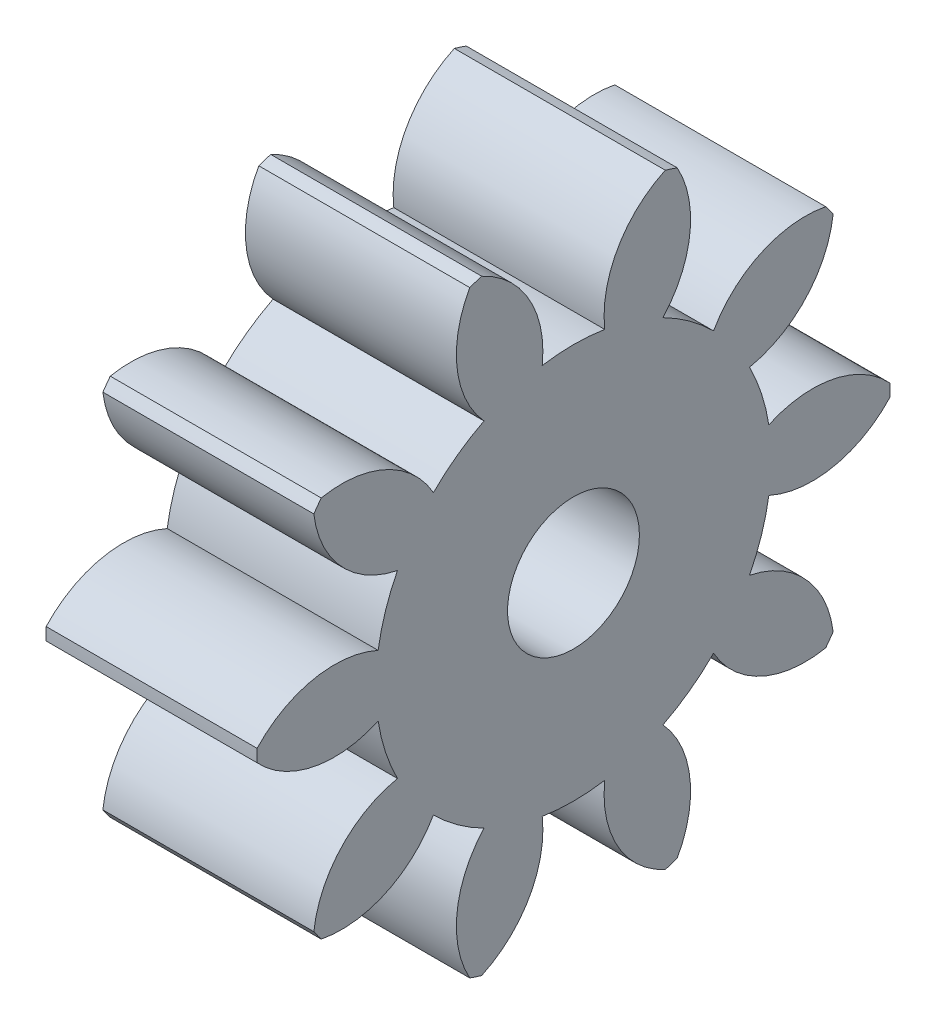
SolidWorks part; units mm, degrees
ref_plane "Plane1" through (0, 0, 0) normal (0, 0, 1) x (1, 0, 0)
ref_plane "Plane2" through (0, 0, 0) normal (0, 1, 0) x (1, 0, 0)
ref_plane "Plane3" through (0, 0, 0) normal (1, 0, 0) x (0, 0, -1)
sketch "HoldingSke" plane through (0, 0, 0) normal (0, 1, 0) x (1, 0, 0)
  line L0 (0, 0) -> (0.9848, -0.1736)
  line L1 (-15, 0) -> (100, 0) construction
  line L2 (0, 0) -> (-2.1039, 2.3779)
  line L3 (0, 0) -> (-11.863, 4.5341)
  line L4 (0, 0) -> (8.5048, 1.4996)
  line L5 (0, 0) -> (-46.8476, -17.4728)
  line L6 (0, 0) -> (-4.9738, -3.3558)
  line L7 (-2.1039, 2.3779) -> (8.6586, 51.2059)
  line L8 (-76.2, 54.61) -> (-75.9, 54.61)
  line L9 (-71.009, 38.7566) -> (-53.1078, 45.2721)
  line L10 (-76.2, 71.12) -> (104.1128, 71.12)
  line L11 (0, 0) -> (-6, 0)
  line L12 (-76.2, 101.6) -> (-76.162, 101.6)
  line L13 (24.9733, 27.94) -> (52.9518, 28.4284)
  line L14 (24.9733, 27.94) -> (24.9743, 27.94)
  line L15 (24.9733, 27.94) -> (100.4006, 29.5858)
  line L16 (-63.627, -1) -> (-12.827, -1)
  circle A0 centre (0, 0) radius 1
  circle A1 centre (0, 0) radius 3.749
  circle A2 centre (0, 0) radius 37.5
  circle A3 centre (0, 0) radius 1
  dimension "MHD" = 7.498
  dimension "Hub_dia" = 75
  dimension "Bore" = 2
  dimension "MBD" = 2
  dimension "Num_teeth" = 10
  dimension "Pitch" = 1
  dimension "Overall_len" = 50
  dimension "Show_teeth" = 10
  dimension "Thickness" = 6
  dimension "OAL" = 50.0001
  dimension "T_dim" = 0.3
  dimension "Ap" = 20
  dimension "H" = 19.05
  dimension "Pitch_radius" = 180.3128
  dimension "Width" = 6
  dimension "Backlash" = 0.038
  dimension "Addendum_fac" = 1
  dimension "Dedendum_fac" = 1.25
  dimension "Clearance_fac" = 0.25
  dimension "Dedendum_add" = 0.001
  dimension "Module" = 1
sketch "BasProSke" plane through (0, 0, 0) normal (0, 1, 0) x (1, 0, 0)
  line L0 (-10, 0) -> (60, 0) construction
  line L1 (0, 0) -> (0, 6)
  line L2 (0, 0) -> (4, 0)
  line L3 (4, 0) -> (4, 6)
  line L4 (4, 6) -> (0, 6)
  dimension "Thickness" = 4
  dimension "Diameter" = 12
revolve "Base-Revolve" add sketch "BasProSke" angle 360 about L0
sketch "TooCutSke" plane through (0, 0, 0) normal (1, 0, 0) x (0, 0, -1)
  line L1 (0, 0) -> (0, 107) construction
  line L2 (0, 0) -> (-0.8485, 4.9275) construction
  line L3 (0, 0) -> (-3.0584, 9.4126) construction
  line L4 (-0.8485, 4.9275) -> (-1.5292, 4.7063) construction
  arc A0 (0.5928, 3.7018) -> (-0.5928, 3.7018) centre (0, 0) ccw
  arc A1 (1.7758, 5.7578) -> (-1.7758, 5.7578) centre (0, 0) ccw
  circle A2 centre (0, 0) radius 5 construction
  circle A3 centre (0, 0) radius 4.6985 construction
  arc A4 (-0.5928, 3.7018) -> (-1.7758, 5.7578) centre (-2.5801, 3.9267) ccw
  arc A5 (1.7758, 5.7578) -> (0.5928, 3.7018) centre (2.5801, 3.9267) ccw
  dimension "Root_dia" = 7.498
  dimension "Overcut_dia" = 12.0508
  dimension "Pitch_dia" = 10
  dimension "Base_dia" = 9.3969
  dimension "Flank_rad" = 2
  dimension "Half_ang" = 18
  dimension "Half_CT" = 0.7157
extrude "ToothCut" cut sketch "TooCutSke" along normal through all
fillet "Breaks" [suppressed] radius 0.02
fillet "RootFillets" [suppressed] radius 0.251
pattern_circular "TeethCuts" count 10 over 360 about axis through (0, 0, 0) along (1, 0, 0) of "ToothCut", "RootFillets", "Breaks"
sketch "HubNeaOneSke" plane through (0, 0, 0) normal (-1, 0, 0) x (0, 0, 1)
  circle A0 centre (0, 0) radius 3.749
  dimension "Diameter" = 7.498
extrude "HubNearOne" [suppressed] add sketch "HubNeaOneSke" along normal blind 46.0001
sketch "HubNeaBotSke" plane through (0, 0, 0) normal (-1, 0, 0) x (0, 0, 1)
  circle A0 centre (0, 0) radius 3.749
  dimension "Diameter" = 7.498
extrude "HubNearBoth" [suppressed] add sketch "HubNeaBotSke" along normal blind 23
ref_plane "FarPln" through (4, 0, 0) normal (1, 0, 0) x (0, 0, -1)
sketch "HubFarSke" plane through (4, 0, 0) normal (1, 0, 0) x (0, 0, -1)
  circle A0 centre (0, 0) radius 3.749
  dimension "Diameter" = 7.498
extrude "HubFar" [suppressed] add sketch "HubFarSke" along normal blind 23
sketch "BorSke" plane through (0, 0, 0) normal (1, 0, 0) x (0, 0, -1)
  circle A0 centre (0, 0) radius 1
  dimension "Diameter" = 2
extrude "Bore" cut sketch "BorSke" along normal mid plane 100.0001
sketch "KeySke" plane through (0, 0, 0) normal (1, 0, 0) x (0, 0, -1)
  line L0 (-0.4, 0) -> (-0.4, 1.3)
  line L1 (-0.4, 1.3) -> (0.4, 1.3)
  line L2 (0.4, 1.3) -> (0.4, 0)
  line L3 (0, 0) -> (0, 34) construction
  line L4 (-0.4, 0) -> (0.4, 0)
  dimension "Offset" = 1.3
  dimension "Width" = 0.8
extrude "Keyway" [suppressed] cut sketch "KeySke" along normal mid plane 100.0001
pattern_circular "Keyway2" [suppressed] count 2 every 90 about axis through (-10, 0, 0) along (1, 0, 0)
sketch "草图1" plane through (4, 0, 0) normal (1, 0, 0) x (0, 0, -1)
  circle A0 centre (0, 0) radius 1.25
  dimension "D1" = 2.5
extrude "切除-拉伸1" cut sketch "草图1" against normal blind 10
equation "' \"Module@HoldingSke\" = 6.35"
equation "' \"Num_teeth@HoldingSke\" = 12"
equation "' \"Ap@HoldingSke\" =  20"
equation "' \"Ap@HoldingSke\" = 20"
equation "' \"Width@HoldingSke\" = 0.5 * 25.4"
equation "' \"Hub_dia@HoldingSke\"= 1 * 25.4"
equation "' \"Hub_dia@HoldingSke\" = 1 * 25.4"
equation "' \"Overall_len@HoldingSke\" = 1.0 * 25.4"
equation "' \"Bore@HoldingSke\" = 0.75 * 25.4"
equation "' \"T_dim@HoldingSke\" = 0.1 * 25.4"
equation "' \"Width@KeySke\" = 0.25 * 25.4"
equation "' \"Show_teeth@HoldingSke\" = 13"
equation "' \"Backlash@HoldingSke\" = 0.009 * 25.4"
equation "' \"Addendum_fac@HoldingSke\" = 1.0"
equation "' \"Dedendum_fac@HoldingSke\" = 1.25"
equation "' \"Dedendum_add@HoldingSke\" = 0.00005 * 25.4"
equation "' \"Clearance_fac@HoldingSke\" = 0.25"
equation "\"Pitch@HoldingSke\" = 1 / \"Module@HoldingSke\""
equation "\"Overcut_dia@TooCutSke\" = (\"Num_teeth@HoldingSke\" + 2 * \"Addendum_fac@HoldingSke\") / \"Pitch@HoldingSke\" + 0.002 * 25.4"
equation "\"Pitch_dia@TooCutSke\" = \"Num_teeth@HoldingSke\" / \"Pitch@HoldingSke\""
equation "\"Base_dia@TooCutSke\" = \"Num_teeth@HoldingSke\" / \"Pitch@HoldingSke\" * cos((\"Ap@HoldingSke\"  * 3.14159265 / 180))"
equation "\"Root_dia@TooCutSke\" = (\"Num_teeth@HoldingSke\" + 2) / \"Pitch@HoldingSke\" - 2 * (\"Addendum_fac@HoldingSke\" + \"Dedendum_fac@HoldingSke\") / \"Pitch@HoldingSke\" - \"Dedendum_add@HoldingSke\" * 2"
equation "\"Half_ang@TooCutSke\" = 180 / \"Num_teeth@HoldingSke\""
equation "\"Half_CT@TooCutSke\" = \"Num_teeth@HoldingSke\" / \"Pitch@HoldingSke\" * sin((3.14159265 / 2 / \"Num_teeth@HoldingSke\")) / 2 - 7 * \"Backlash@HoldingSke\" / 4"
equation "\"Flank_rad@TooCutSke\" = \"Num_teeth@HoldingSke\" / \"Pitch@HoldingSke\" / 5"
equation "\"Radius@RootFillets\" = \"Clearance_fac@HoldingSke\" / \"Pitch@HoldingSke\" + \"Dedendum_add@HoldingSke\""
equation "\"Break_rad@Breaks\" = 0.02 / \"Pitch@HoldingSke\""
equation "\"Thickness@HoldingSke\" = \"Width@HoldingSke\""
equation "\"OAL@HoldingSke\" = \"Thickness@HoldingSke\""
equation "\"MHD@HoldingSke\" = (\"Num_teeth@HoldingSke\" + 2) / \"Pitch@HoldingSke\" - 2 * (\"Addendum_fac@HoldingSke\" + \"Dedendum_fac@HoldingSke\")  / \"Pitch@HoldingSke\" - \"Dedendum_add@HoldingSke\" * 2"
equation "\"MBD@HoldingSke\" = (\"Num_teeth@HoldingSke\" + 2) / \"Pitch@HoldingSke\" - 2 * (\"Addendum_fac@HoldingSke\" + \"Dedendum_fac@HoldingSke\")  / \"Pitch@HoldingSke\" - \"Dedendum_add@HoldingSke\" * 2 - 0.002 * 25.4"
equation "\"MHD@HoldingSke\" = ((sgn( \"MHD@HoldingSke\" - \"Hub_dia@HoldingSke\" )-1)*( \"MHD@HoldingSke\" - \"Hub_dia@HoldingSke\" ))/-2+ \"Hub_dia@HoldingSke\""
equation "\"MBD@HoldingSke\" = ((sgn( \"MBD@HoldingSke\" - \"Bore@HoldingSke\" )-1)*( \"MBD@HoldingSke\" - \"Bore@HoldingSke\" ))/-2+ \"Bore@HoldingSke\""
equation "\"OAL@HoldingSke\" = ((sgn( \"OAL@HoldingSke\" - \"Overall_len@HoldingSke\" )+1)*( \"OAL@HoldingSke\" - \"Overall_len@HoldingSke\" ))/2 + \"Overall_len@HoldingSke\" + 0.000002 * 25.4"
equation "\"Num_teeth@TeethCuts\" = int( \"Show_teeth@HoldingSke\" ) + 1"
equation "\"Num_teeth@TeethCuts\" = ((sgn( \"Num_teeth@TeethCuts\" - \"Num_teeth@HoldingSke\" )-1)*( \"Num_teeth@TeethCuts\" - \"Num_teeth@HoldingSke\" ))/-2+ \"Num_teeth@HoldingSke\""
equation "\"Num_teeth@TeethCuts\" = ((sgn( \"Num_teeth@TeethCuts\" - 2.0)+1)*( \"Num_teeth@TeethCuts\" - 2.0))/2 +2.0"
equation "\"Angle@TeethCuts\" = 360.0 / \"Num_teeth@HoldingSke\""
equation "\"Diameter@BasProSke\" = (\"Num_teeth@HoldingSke\" + 2 * \"Addendum_fac@HoldingSke\") / \"Pitch@HoldingSke\""
equation "\"Thickness@BasProSke\"=\"Thickness@HoldingSke\"-2"
equation "' \"Fillet_rad@BasProSke\" =  \"Thickness@HoldingSke\" * 0.05"
equation "' \"Fillet_rad@BasProSke\" = \"Thickness@HoldingSke\" * 0.05"
equation "\"MHD@HoldingSke\" = ((sgn( \"MHD@HoldingSke\" - \"Root_dia@TooCutSke\" )-1)*( \"MHD@HoldingSke\" - \"Root_dia@TooCutSke\" ))/-2+ \"Root_dia@TooCutSke\""
equation "\"Diameter@HubNeaOneSke\" = \"MHD@HoldingSke\""
equation "\"Length@HubNearOne\" = \"OAL@HoldingSke\" - \"Thickness@BasProSke\""
equation "\"Diameter@HubNeaBotSke\" = \"MHD@HoldingSke\""
equation "\"Length@HubNearBoth\" = ( \"OAL@HoldingSke\" - \"Thickness@BasProSke\" ) / 2.0"
equation "\"Thickness@FarPln\" = \"Thickness@BasProSke\""
equation "\"Diameter@HubFarSke\" = \"MHD@HoldingSke\""
equation "\"Length@HubFar\" = ( \"OAL@HoldingSke\" - \"Thickness@BasProSke\" ) / 2.0"
equation "\"Diameter@BorSke\" = \"MBD@HoldingSke\""
equation "\"D1@Bore\" = \"OAL@HoldingSke\" * 2.0"
equation "\"D1@Keyway\" = \"OAL@HoldingSke\" * 2.0"
equation "\"Offset@KeySke\" = \"T_dim@HoldingSke\" + \"MBD@HoldingSke\" / 2.0"
